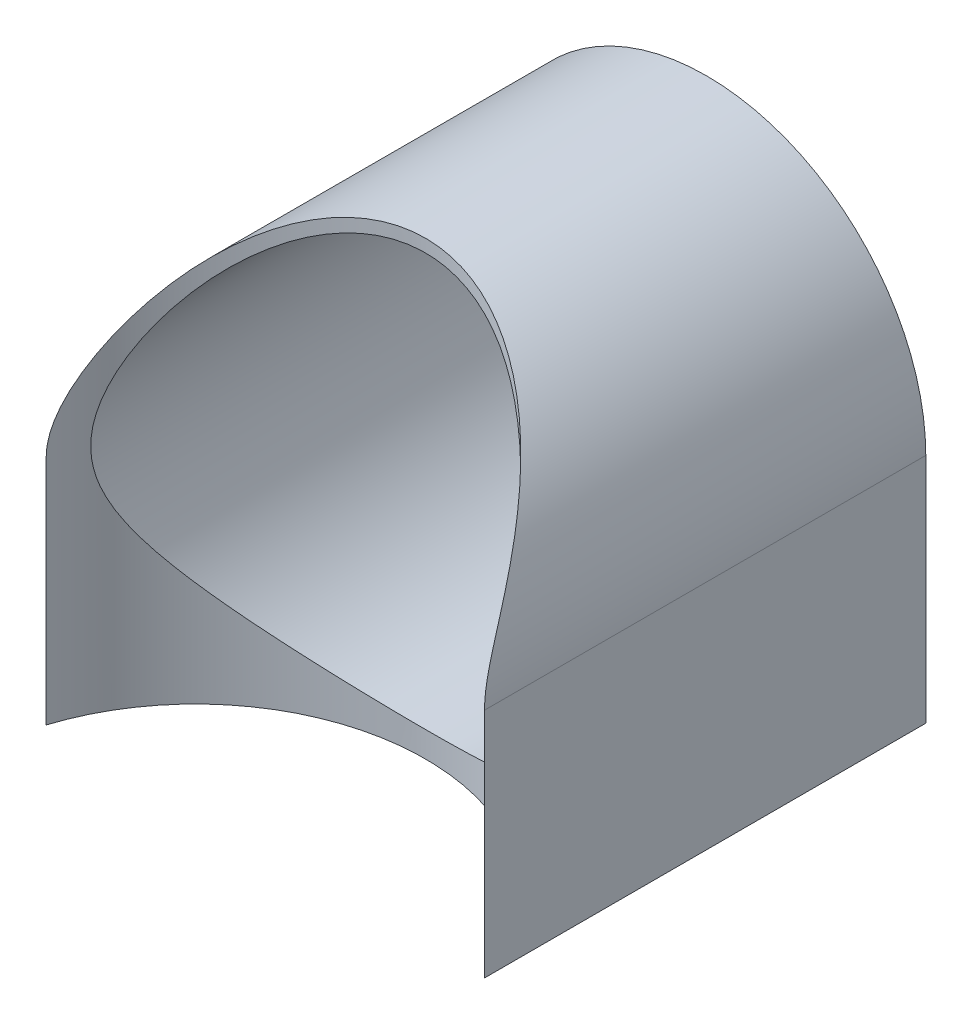
SolidWorks part; units mm, degrees
ref_plane "Front Plane" through (0, 0, 0) normal (0, 0, 1) x (1, 0, 0)
ref_plane "Top Plane" through (0, 0, 0) normal (0, 1, 0) x (1, 0, 0)
ref_plane "Right Plane" through (0, 0, 0) normal (1, 0, 0) x (0, 0, -1)
sketch "Sketch1" plane through (0, 0, 0) normal (0, 0, 1) x (1, 0, 0)
  circle A0 centre (0, 200) radius 15.85 construction
  circle A1 centre (0, 200) radius 15.85 construction
  circle A2 centre (0, 200) radius 16.15
  circle A3 centre (0, 200) radius 17.15
  dimension "D1" = 0.3
  dimension "D2" = 1.3
extrude "Boss-Extrude1" add sketch "Sketch1" against normal blind 40
sketch "Sketch3" plane through (0, 0, -40) normal (0, 0, -1) x (-1, 0, 0)
  line L0 (17.15, 200) -> (17.15, 182.85)
  line L1 (17.15, 182.85) -> (0, 182.85)
  line L2 (0, 182.85) -> (-17.15, 182.85)
  line L3 (-17.15, 182.85) -> (-17.15, 200)
  line L5 (-17.15, 182.85) -> (17.15, 182.85)
  line L6 (-17.15, 182.85) -> (-17.15, 181.85)
  line L7 (-17.15, 181.85) -> (17.15, 181.85)
  line L8 (17.15, 182.85) -> (17.15, 181.85)
  circle A0 centre (0, 200) radius 17.15 construction
  circle M6 centre (0, 200) radius 17.15
  dimension "D1" = 1
extrude "Boss-Extrude2" add sketch "Sketch3" against normal blind 40 contours L8 L1 L2 L6 L7 | L1 L0 M6 | L3 L2 M6
sketch "Sketch2" plane through (0, 550, 0) normal (0, 1, 0) x (1, 0, 0)
  circle A0 centre (0, 0) radius 18 construction
  circle A1 centre (0, 0) radius 18
extrude "Cut-Extrude1" cut sketch "Sketch2" against normal through all
